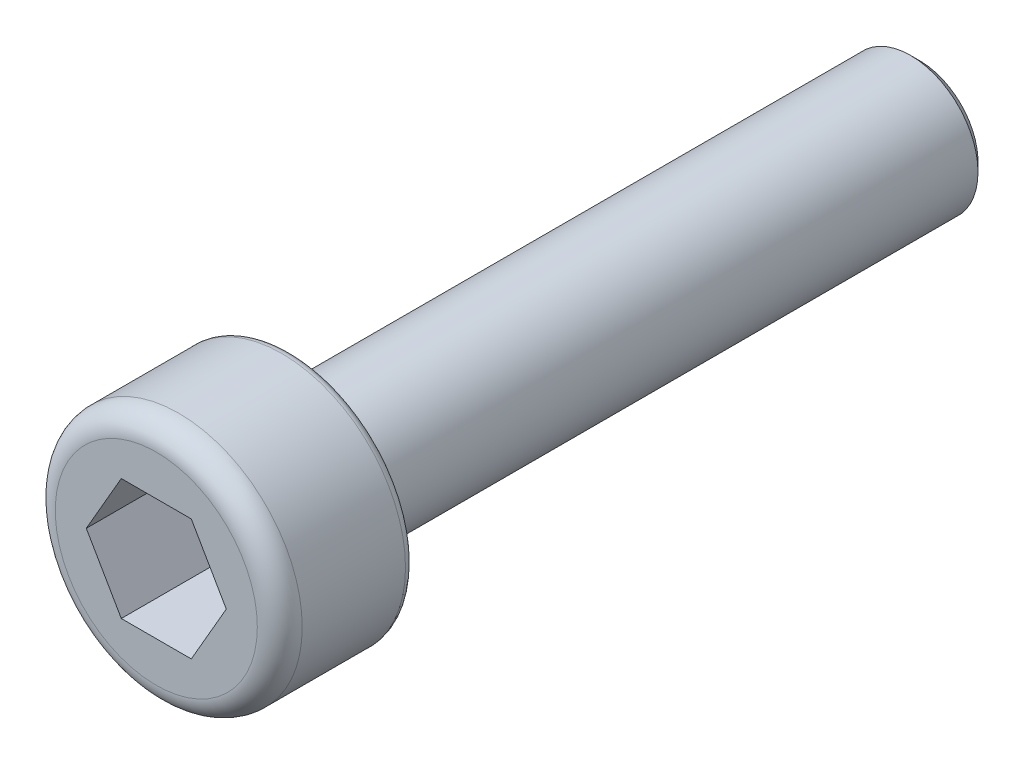
SolidWorks part; units mm, degrees
ref_plane "前视" through (0, 0, 0) normal (0, 0, 1) x (1, 0, 0)
ref_plane "上视" through (0, 0, 0) normal (0, 1, 0) x (1, 0, 0)
ref_plane "右视" through (0, 0, 0) normal (1, 0, 0) x (0, 0, -1)
sketch "草图1" plane through (0, 0, 0) normal (0, 0, 1) x (1, 0, 0)
  circle A0 centre (0, 0) radius 2.75
  dimension "D1" = 5.5
extrude "凸台-拉伸1" add sketch "草图1" along normal blind 3
fillet "圆角1" radius 0.5 1 edges at (2.75, 0, 3)
sketch "草图2" plane through (0, 0, 3) normal (0, 0, 1) x (1, 0, 0)
  line L1 (1.5588, 0) -> (0.7794, 1.35)
  line L2 (0.7794, 1.35) -> (-0.7794, 1.35)
  line L3 (-0.7794, 1.35) -> (-1.5588, 0)
  line L4 (-1.5588, 0) -> (-0.7794, -1.35)
  line L5 (-0.7794, -1.35) -> (0.7794, -1.35)
  line L6 (0.7794, -1.35) -> (1.5588, 0)
  circle A0 centre (0, 0) radius 1.35 construction
  dimension "D1" = 2.7
extrude "切除-拉伸1" cut sketch "草图2" against normal blind 2
sketch "草图3" plane through (0, 0, 0) normal (0, 0, -1) x (-1, 0, 0)
  circle A0 centre (0, 0) radius 1.5
  dimension "D1" = 3
extrude "凸台-拉伸2" add sketch "草图3" along normal blind 14
chamfer "倒角1" distance 0.2 angle 45 1 edges at (-1.5, 0, -14)
fillet "圆角2" radius 0.2 1 edges at (2.75, 0, 0)
